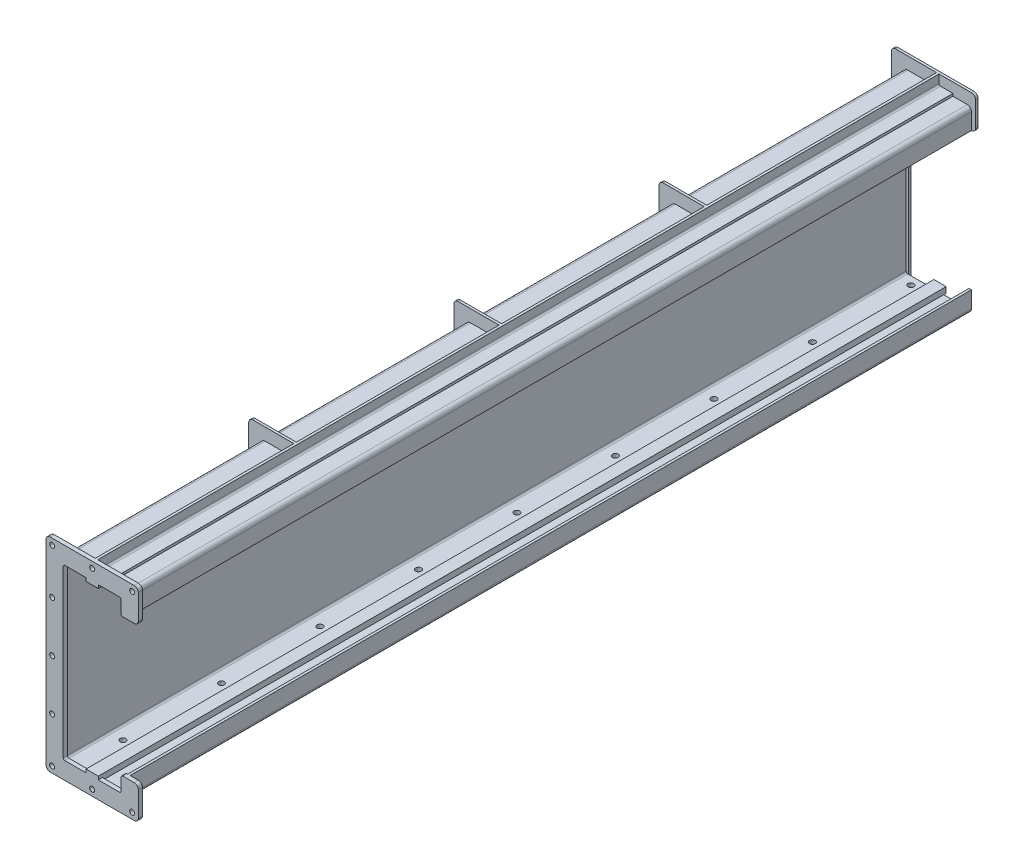
SolidWorks part; units mm, degrees
material "普通碳钢"
ref_plane "前视基准面" through (0, 0, 0) normal (0, 0, 1) x (1, 0, 0)
ref_plane "上视基准面" through (0, 0, 0) normal (0, 1, 0) x (1, 0, 0)
ref_plane "右视基准面" through (0, 0, 0) normal (1, 0, 0) x (0, 0, -1)
sketch "草图1" plane through (0, 0, 0) normal (0, 0, 1) x (1, 0, 0)
  line L0 (10, 430) -> (155, 430)
  line L1 (10, 0) -> (155, 0)
  line L2 (0, 10) -> (0, 426)
  line L3 (10, 436) -> (155, 436)
  line L4 (165, 10) -> (165, 50)
  line L5 (159, 10) -> (159, 50)
  line L6 (10, 6) -> (155, 6)
  line L7 (6, 10) -> (6, 426)
  line L8 (159, 386) -> (165, 386)
  line L9 (159, 50) -> (165, 50)
  line L10 (159, 386) -> (159, 426)
  line L11 (165, 386) -> (165, 426)
  line L12 (159, 10) -> (159, 426) construction
  line L14 (165, 10) -> (165, 426) construction
  arc A0 (155, 0) -> (165, 10) centre (155, 10) ccw
  arc A1 (10, 0) -> (0, 10) centre (10, 10) cw
  arc A2 (155, 436) -> (165, 426) centre (155, 426) cw
  arc A3 (0, 426) -> (10, 436) centre (10, 426) cw
  arc A4 (155, 430) -> (159, 426) centre (155, 426) cw
  arc A5 (155, 6) -> (159, 10) centre (155, 10) ccw
  arc A6 (10, 6) -> (6, 10) centre (10, 10) cw
  arc A7 (6, 426) -> (10, 430) centre (10, 426) cw
  point P9 (0, 0)
  point P12 (165, 436)
  point P15 (0, 436)
  dimension "D3" = 10
  dimension "D1" = 165
  dimension "D2" = 436
  dimension "D5" = 50
  dimension "D6" = 50
  dimension "D4" = 6
extrude "凸台-拉伸1" add sketch "草图1" along normal blind 2050
sketch "草图2" plane through (0, 0, 2050) normal (0, 0, 1) x (1, 0, 0)
  line L0 (165, 386) -> (165, 426) construction
  line L1 (185, 466) -> (-20, 466)
  line L2 (195, 456) -> (195, 396)
  line L3 (185, -30) -> (-20, -30)
  line L4 (-30, 456) -> (-30, -20)
  line L6 (0, 426) -> (0, 10) construction
  line L7 (10, 0) -> (155, 0) construction
  line L20 (157, 50) -> (185, 50)
  line L21 (157, 386) -> (185, 386)
  line L22 (195, 40) -> (195, -20)
  line L24 (153, 50) -> (153, 10)
  line L25 (153, 46) -> (153, 16)
  line L27 (155, 12) -> (10, 12)
  line L28 (149, 12) -> (16, 12)
  line L30 (12, 10) -> (12, 426)
  line L31 (12, 16) -> (12, 420)
  line L33 (10, 424) -> (155, 424)
  line L34 (16, 424) -> (149, 424)
  line L36 (153, 426) -> (153, 386)
  line L37 (153, 420) -> (153, 390)
  arc A1 (185, 386) -> (195, 396) centre (185, 396) ccw
  arc A2 (185, 50) -> (195, 40) centre (185, 40) cw
  arc A3 (195, -20) -> (185, -30) centre (185, -20) cw
  arc A4 (-20, -30) -> (-30, -20) centre (-20, -20) cw
  arc A5 (185, 466) -> (195, 456) centre (185, 456) cw
  arc A6 (-20, 466) -> (-30, 456) centre (-20, 456) ccw
  arc A7 (153, 390) -> (157, 386) centre (157, 390) ccw
  arc A8 (153, 46) -> (157, 50) centre (157, 46) cw
  arc A9 (153, 16) -> (149, 12) centre (149, 16) cw
  arc A10 (16, 12) -> (12, 16) centre (16, 16) cw
  arc A11 (16, 424) -> (12, 420) centre (16, 420) ccw
  arc A12 (153, 420) -> (149, 424) centre (149, 420) ccw
  point P45 (195, 50)
  dimension "D5" = 10
  dimension "D10" = 4
  dimension "D1" = 30
  dimension "D2" = 6
  dimension "D3" = 30
  dimension "D4" = 30
  dimension "D6" = 6
  dimension "D7" = 6
  dimension "D8" = 6
  dimension "D9" = 6
extrude "凸台-拉伸2" add sketch "草图2" along normal blind 10 separate body
ref_plane "基准面1" through (0, 0, 1560) normal (0, 0, 1) x (1, 0, 0)
ref_plane "基准面2" through (0, 0, 1060) normal (0, 0, 1) x (1, 0, 0)
ref_plane "基准面3" through (0, 0, 560) normal (0, 0, 1) x (1, 0, 0)
sketch "草图3" plane through (0, 436, 0) normal (0, 1, 0) x (1, 0, 0)
  line L1 (120, 0) -> (80, 0)
  line L2 (120, 0) -> (120, -2050)
  line L4 (80, 0) -> (80, -2050)
  line L5 (155, 0) -> (10, 0) construction
  line L6 (0, -2050) -> (0, 0) construction
  line L7 (120, -2050) -> (80, -2050)
  line L8 (155, -2050) -> (10, -2050) construction
  dimension "D1" = 40
  dimension "D2" = 80
extrude "凸台-拉伸3" add sketch "草图3" along normal blind 6 separate body
sketch "草图4" plane through (0, 442, 0) normal (0, 1, 0) x (1, 0, 0)
  line L0 (80, -2050) -> (120, -2050) construction
  line L1 (80, 0) -> (86, 0)
  line L2 (80, 0) -> (80, -2050)
  line L3 (80, -2050) -> (86, -2050)
  line L4 (86, 0) -> (86, -2050)
  dimension "D1" = 6
extrude "凸台-拉伸4" add sketch "草图4" along normal blind 24
fillet "圆角1" radius 4 1 edges at (86, 442, 1025)
fillet "圆角2" radius 10 1 edges at (80, 436, 1025)
sketch "草图5" plane through (0, 0, 1560) normal (0, 0, 1) x (1, 0, 0)
  line L0 (0, 0) -> (-20, 0)
  line L1 (0, 0) -> (0, 426)
  line L2 (10, 436) -> (80, 436)
  line L4 (80, 466) -> (80, 436)
  line L22 (90, 442) -> (120, 442)
  line L23 (86, 466) -> (86, 446)
  line L24 (185, 466) -> (86, 466)
  line L25 (195, 396) -> (195, 456)
  line L26 (157, 386) -> (185, 386)
  line L27 (153, 420) -> (153, 390)
  line L29 (16, 424) -> (149, 424)
  line L31 (12, 16) -> (12, 420)
  line L33 (149, 12) -> (16, 12)
  line L35 (153, 46) -> (153, 16)
  line L36 (185, 50) -> (157, 50)
  line L37 (195, -20) -> (195, 40)
  line L38 (-20, -30) -> (185, -30)
  line L39 (-30, 456) -> (-30, -20)
  line L40 (80, 466) -> (-20, 466)
  line L41 (80, 446) -> (80, 466)
  line L42 (120, 436) -> (90, 436)
  line L43 (120, 442) -> (120, 436)
  line L46 (80, 466) -> (-20, 466)
  line L61 (-30, 456) -> (-30, 10)
  arc A0 (-20, 0) -> (-30, 10) centre (-20, 10) cw
  arc A1 (10, 436) -> (0, 426) centre (10, 426) ccw construction
  arc A2 (10, 436) -> (0, 426) centre (10, 426) ccw
  arc A8 (86, 446) -> (90, 442) centre (90, 446) ccw
  arc A9 (195, 456) -> (185, 466) centre (185, 456) ccw
  arc A10 (185, 386) -> (195, 396) centre (185, 396) ccw
  arc A11 (195, 40) -> (185, 50) centre (185, 40) ccw
  arc A12 (185, -30) -> (195, -20) centre (185, -20) ccw
  arc A13 (-30, -20) -> (-20, -30) centre (-20, -20) ccw
  arc A14 (-20, 466) -> (-30, 456) centre (-20, 456) ccw
  arc A15 (80, 446) -> (90, 436) centre (90, 446) ccw
  arc A22 (-20, 466) -> (-30, 456) centre (-20, 456) ccw
  arc A34 (153, 390) -> (157, 386) centre (157, 390) ccw
  arc A36 (153, 420) -> (149, 424) centre (149, 420) ccw
  arc A38 (16, 424) -> (12, 420) centre (16, 420) ccw
  arc A40 (12, 16) -> (16, 12) centre (16, 16) ccw
  arc A42 (149, 12) -> (153, 16) centre (149, 16) ccw
  arc A44 (157, 50) -> (153, 46) centre (157, 46) ccw
  dimension "D2" = 10
  dimension "D1" = 0
extrude "凸台-拉伸5" add sketch "草图5" along normal blind 6
sketch "草图6" plane through (0, 0, 1060) normal (0, 0, 1) x (1, 0, 0)
  line L8 (0, 0) -> (0, 10)
  line L9 (-20, 0) -> (0, 0)
  line L10 (-30, 456) -> (-30, 10)
  line L11 (80, 466) -> (-20, 466)
  line L12 (80, 446) -> (80, 466)
  line L13 (80, 436) -> (80, 446)
  line L14 (10, 436) -> (80, 436)
  line L15 (0, 10) -> (0, 426)
  line L16 (0, 0) -> (0, 10)
  line L17 (-20, 0) -> (0, 0)
  line L18 (-30, 456) -> (-30, 10)
  line L19 (80, 466) -> (-20, 466)
  line L20 (80, 446) -> (80, 466)
  line L21 (80, 436) -> (80, 446)
  line L22 (10, 436) -> (80, 436)
  line L23 (0, 10) -> (0, 426)
  arc A3 (-30, 10) -> (-20, 0) centre (-20, 10) ccw
  arc A4 (-20, 466) -> (-30, 456) centre (-20, 456) ccw
  arc A5 (10, 436) -> (0, 426) centre (10, 426) ccw
  arc A6 (-30, 10) -> (-20, 0) centre (-20, 10) ccw
  arc A7 (-20, 466) -> (-30, 456) centre (-20, 456) ccw
  arc A8 (10, 436) -> (0, 426) centre (10, 426) ccw
  dimension "D1" = 0
extrude "凸台-拉伸6" add sketch "草图6" along normal blind 6
sketch "草图7" plane through (0, 0, 560) normal (0, 0, 1) x (1, 0, 0)
  line L6 (0, 10) -> (0, 426)
  line L9 (0, 0) -> (0, 10)
  line L10 (-20, 0) -> (0, 0)
  line L11 (-30, 456) -> (-30, 10)
  line L12 (80, 466) -> (-20, 466)
  line L14 (80, 436) -> (80, 446)
  line L15 (0, 10) -> (0, 426)
  line L17 (0, 0) -> (0, 10)
  line L18 (-20, 0) -> (0, 0)
  line L19 (-30, 456) -> (-30, 10)
  line L20 (80, 466) -> (-20, 466)
  line L22 (80, 436) -> (80, 446)
  line L24 (80, 446) -> (80, 466)
  line L25 (80, 446) -> (80, 466)
  line L26 (10, 436) -> (80, 436)
  line L27 (10, 436) -> (80, 436)
  arc A3 (10, 436) -> (0, 426) centre (10, 426) ccw
  arc A4 (-30, 10) -> (-20, 0) centre (-20, 10) ccw
  arc A5 (-20, 466) -> (-30, 456) centre (-20, 456) ccw
  arc A7 (-30, 10) -> (-20, 0) centre (-20, 10) ccw
  arc A8 (-20, 466) -> (-30, 456) centre (-20, 456) ccw
  arc A10 (10, 436) -> (0, 426) centre (10, 426) ccw
  dimension "D1" = 0
extrude "凸台-拉伸7" add sketch "草图7" along normal blind 6
sketch "草图8" plane through (0, 0, 0) normal (0, 0, -1) x (-1, 0, 0)
  line L0 (-12, 0) -> (30, 0)
  line L1 (-10, 0) -> (-155, 0) construction
  line L2 (-12, 420) -> (-12, 0)
  line L3 (-165, 386) -> (-165, 426) construction
  line L14 (-153, 16) -> (-153, 46)
  line L16 (-16, 12) -> (-149, 12)
  line L18 (-185, 386) -> (-157, 386)
  line L19 (-195, 456) -> (-195, 396)
  line L20 (20, 466) -> (-185, 466)
  line L21 (30, -20) -> (30, 456)
  line L22 (-185, -30) -> (20, -30)
  line L23 (-195, 40) -> (-195, -20)
  line L24 (-157, 50) -> (-185, 50)
  line L25 (-12, 420) -> (-12, 16)
  line L27 (-149, 424) -> (-16, 424)
  line L28 (-149, 424) -> (-16, 424)
  line L29 (-153, 390) -> (-153, 420)
  line L30 (-153, 390) -> (-153, 420)
  line L34 (-157, 386) -> (-165, 386)
  line L35 (-175, 456) -> (-175, 396)
  line L36 (20, 466) -> (-165, 466)
  line L37 (30, 0) -> (30, 456)
  arc A0 (-165, 386) -> (-175, 396) centre (-165, 396) cw
  arc A1 (-165, 466) -> (-175, 456) centre (-165, 456) ccw
  arc A6 (-195, 396) -> (-185, 386) centre (-185, 396) ccw
  arc A7 (-185, 466) -> (-195, 456) centre (-185, 456) ccw
  arc A8 (30, 456) -> (20, 466) centre (20, 456) ccw
  arc A9 (20, -30) -> (30, -20) centre (20, -20) ccw
  arc A10 (-195, -20) -> (-185, -30) centre (-185, -20) ccw
  arc A11 (-185, 50) -> (-195, 40) centre (-185, 40) ccw
  arc A14 (30, 456) -> (20, 466) centre (20, 456) ccw
  arc A21 (-157, 386) -> (-153, 390) centre (-157, 390) ccw
  arc A22 (-157, 386) -> (-153, 390) centre (-157, 390) ccw
  arc A23 (-153, 46) -> (-157, 50) centre (-157, 46) ccw
  arc A25 (-153, 16) -> (-149, 12) centre (-149, 16) ccw
  arc A27 (-16, 12) -> (-12, 16) centre (-16, 16) ccw
  arc A29 (-12, 420) -> (-16, 424) centre (-16, 420) ccw
  arc A30 (-12, 420) -> (-16, 424) centre (-16, 420) ccw
  arc A31 (-149, 424) -> (-153, 420) centre (-149, 420) ccw
  arc A32 (-149, 424) -> (-153, 420) centre (-149, 420) ccw
  dimension "D3" = 10
  dimension "D2" = 10
  dimension "D1" = 0
extrude "凸台-拉伸8" add sketch "草图8" along normal blind 6
sketch "草图9" plane through (0, 0, 0) normal (0, -1, 0) x (1, 0, 0)
  line L0 (10, 2050) -> (155, 2050) construction
  line L1 (-30, -6) -> (150, -6)
  line L2 (-30, -6) -> (-30, 2050)
  line L3 (-30, 2050) -> (150, 2050)
  line L4 (150, -6) -> (150, 2050)
  dimension "D1" = 180
extrude "凸台-拉伸9" add sketch "草图9" along normal blind 6
sketch "草图10" plane through (0, 0, 2060) normal (0, 0, 1) x (1, 0, 0)
  line L1 (67.5, 6) -> (97.5, 6)
  line L2 (67.5, 6) -> (67.5, 20)
  line L3 (67.5, 20) -> (97.5, 20)
  line L4 (97.5, 6) -> (97.5, 20)
  line L7 (67.5, 430) -> (97.5, 430)
  line L8 (67.5, 430) -> (67.5, 416)
  line L9 (67.5, 416) -> (97.5, 416)
  line L10 (97.5, 430) -> (97.5, 416)
  line L11 (6, 10) -> (6, 426) construction
  line L12 (10, 430) -> (155, 430) construction
  line L13 (155, 6) -> (10, 6) construction
  dimension "D1" = 30
  dimension "D2" = 14
  dimension "D3" = 61.5
  dimension "D4" = 14
  dimension "D5" = 30
extrude "凸台-拉伸10" add sketch "草图10" against normal up to surface (2066 mm away)
sketch "草图11" plane through (0, 6, 0) normal (0, 1, 0) x (1, 0, 0)
  line L0 (127.5, 0) -> (127.5, -2050.2156) construction
  line L1 (155, 0) -> (97.5, 0) construction
  line L2 (37.5, 0) -> (37.5, -2050.2156) construction
  line L3 (67.5, 0) -> (12, 0) construction
  line L4 (97.5, 0) -> (97.5, -2050) construction
  line L5 (67.5, 0) -> (67.5, -2050) construction
  line L6 (10, -20) -> (162.8861, -20) construction
  line L7 (10, -2050) -> (10, 0) construction
  line L8 (10, -260) -> (162.8861, -260) construction
  line L9 (10, -500) -> (162.8861, -500) construction
  line L10 (10, -740) -> (162.8861, -740) construction
  line L11 (10, -980) -> (162.8861, -980) construction
  line L12 (10, -1220) -> (162.8861, -1220) construction
  line L13 (10, -1460) -> (162.8861, -1460) construction
  line L14 (10, -1700) -> (162.8861, -1700) construction
  line L15 (10, -1940) -> (162.8861, -1940) construction
  circle A0 centre (37.5, -20) radius 7
  circle A1 centre (127.5, -20) radius 7
  circle A2 centre (37.5, -260) radius 7
  circle A3 centre (127.5, -260) radius 7
  circle A4 centre (37.5, -500) radius 7
  circle A5 centre (127.5, -500) radius 7
  circle A6 centre (37.5, -740) radius 7
  circle A7 centre (127.5, -740) radius 7
  circle A8 centre (37.5, -980) radius 7
  circle A9 centre (127.5, -980) radius 7
  circle A10 centre (37.5, -1220) radius 7
  circle A11 centre (127.5, -1220) radius 7
  circle A12 centre (37.5, -1460) radius 7
  circle A13 centre (127.5, -1460) radius 7
  circle A14 centre (37.5, -1700) radius 7
  circle A15 centre (127.5, -1700) radius 7
  circle A16 centre (37.5, -1940) radius 7
  circle A17 centre (127.5, -1940) radius 7
  dimension "D4" = 14
  dimension "D1" = 30
  dimension "D2" = 30
  dimension "D3" = 20
  dimension "D6" = 240
  dimension "D5" = 9
extrude "切除-拉伸1" cut sketch "草图11" against normal through all
sketch "草图13" plane through (0, 0, 2060) normal (0, 0, 1) x (1, 0, 0)
  line L2 (185, 451) -> (-20, 451)
  line L3 (185, 451) -> (-20, 451) construction
  line L5 (-15, 456) -> (-15, -20)
  line L6 (-15, 456) -> (-15, -20) construction
  line L8 (-20, -15) -> (185, -15)
  line L9 (-20, -15) -> (185, -15) construction
  line L10 (185, 341) -> (-20, 341) construction
  line L11 (180, -20) -> (180, 40)
  line L12 (180, -20) -> (180, 456) construction
  line L13 (-20, 95) -> (185, 95) construction
  circle A0 centre (82.5, -15) radius 6
  circle A1 centre (-15, -15) radius 6
  circle A2 centre (180, -15) radius 6
  circle A3 centre (-15, 218) radius 6
  circle A4 centre (-15, 451) radius 6
  circle A5 centre (82.5, 451) radius 6
  circle A6 centre (180, 451) radius 6
  circle A7 centre (-15, 341) radius 6
  circle A8 centre (-15, 95) radius 6
  dimension "D5" = 110
  dimension "D7" = 12
  dimension "D1" = 15
  dimension "D2" = 15
  dimension "D3" = 15
  dimension "D4" = 15
  dimension "D6" = 110
extrude "切除-拉伸2" cut sketch "草图13" against normal blind 10
